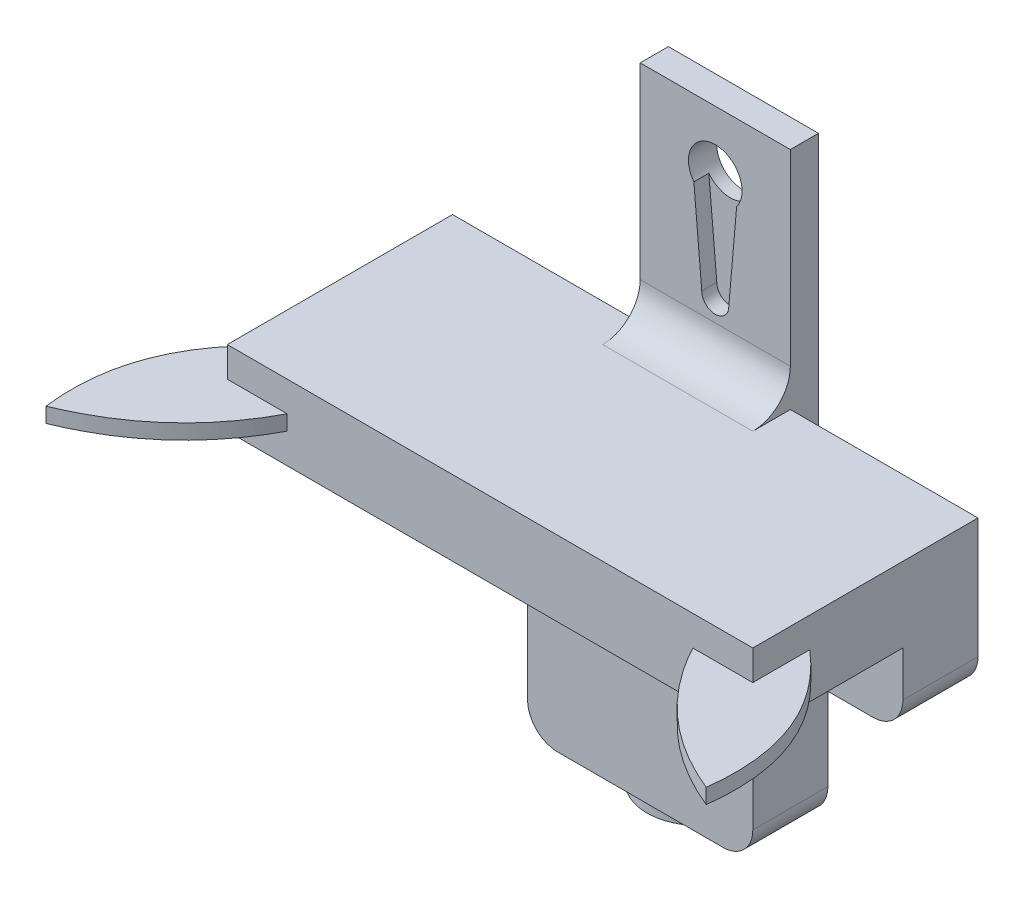
SolidWorks part; units mm, degrees
ref_plane "Front Plane" through (0, 0, 0) normal (0, 0, 1) x (1, 0, 0)
ref_plane "Top Plane" through (0, 0, 0) normal (0, 1, 0) x (1, 0, 0)
ref_plane "Right Plane" through (0, 0, 0) normal (1, 0, 0) x (0, 0, -1)
sketch "Sketch3" plane through (0, 0, 0) normal (0, 0, 1) x (1, 0, 0)
  line L1 (-10, 25) -> (10, 25)
  line L2 (-10, 25) -> (-10, -25)
  line L3 (-10, -25) -> (10, -25)
  line L4 (10, 25) -> (10, -25)
  line L5 (-10, 25) -> (10, -25) construction
  line L6 (-10, -25) -> (10, 25) construction
  point P0 (0, 0)
  dimension "D1" = 20
  dimension "D2" = 50
extrude "Boss-Extrude3" add sketch "Sketch3" along normal blind 5
sketch "Sketch4" plane through (0, 0, 5) normal (0, 0, 1) x (1, 0, 0)
  line L0 (-1.8, 2.7957) -> (1.8, 2.7957)
  line L1 (-2.85, 14.85) -> (2.85, 14.85)
  line L2 (-2.85, 14.85) -> (-1.8, 2.7957)
  line L3 (2.85, 14.85) -> (1.8, 2.7957)
  line L4 (10, -25) -> (10, 25) construction
  line L7 (10, 25) -> (-10, 25) construction
  circle A0 centre (0, 17) radius 3.57
  arc A1 (-1.8, 2.7957) -> (1.8, 2.7957) centre (0, 2.7957) ccw
  dimension "D1" = 7.14
  dimension "D2" = 3.6
  dimension "D3" = 5.7
  dimension "D4" = 12.1
  dimension "D5" = 12.1
  dimension "D6" = 10
  dimension "D7" = 8
extrude "Cut-Extrude2" cut sketch "Sketch4" against normal blind 2 contours L0 A1 | A0 L2 L0 L3
sketch "Sketch6" plane through (0, 0, 3) normal (0, 0, 1) x (1, 0, 0)
  line L0 (10, 25) -> (-10, 25) construction
  line L1 (-10, 25) -> (-10, -25) construction
  circle A0 centre (0, 17) radius 3.57
  dimension "D1" = 7.14
  dimension "D2" = 8
  dimension "D3" = 10
extrude "Cut-Extrude3" cut sketch "Sketch6" against normal blind 3
sketch "Sketch8" plane through (10, 0, 0) normal (1, 0, 0) x (0, 0, -1)
  line L6 (0, 25) -> (-1.25, 25)
  line L7 (0, 25) -> (0, -25)
  line L8 (0, -25) -> (-1.25, -25)
  line L9 (-1.25, 25) -> (-1.25, -25)
  dimension "D2" = 1.25
extrude "Cut-Extrude5" cut sketch "Sketch8" against normal blind 30
sketch "Sketch9" plane through (0, 0, 5) normal (0, 0, 1) x (1, 0, 0)
  line L1 (-35, -25) -> (35, -25)
  line L2 (-35, -25) -> (-35, -5)
  line L3 (-35, -5) -> (35, -5)
  line L4 (35, -25) -> (35, -5)
  line L5 (-10, 25) -> (-10, -25) construction
  dimension "D1" = 20
  dimension "D2" = 70
  dimension "D3" = 25
extrude "Boss-Extrude4" add sketch "Sketch9" along normal blind 20
sketch "Sketch10" plane through (0, 0, 25) normal (0, 0, 1) x (1, 0, 0)
  line L0 (35, -25) -> (35, -5) construction
  line L1 (-35, -25) -> (35, -25)
  line L2 (-35, -25) -> (-35, -15)
  line L3 (-35, -15) -> (35, -15)
  line L4 (35, -25) -> (35, -15)
  dimension "D1" = 10
  dimension "D2" = 70
extrude "Cut-Extrude6" cut sketch "Sketch10" against normal blind 10
sketch "Sketch11" plane through (0, -25, 0) normal (0, -1, 0) x (-1, 0, 0)
  line L1 (15, -15) -> (-15, -15)
  line L2 (15, -15) -> (15, -5)
  line L3 (15, -5) -> (-15, -5)
  line L4 (-15, -15) -> (-15, -5)
  line L9 (35, -15) -> (35, -5) construction
  dimension "D1" = 10
  dimension "D2" = 30
  dimension "D3" = 20
extrude "Boss-Extrude5" add sketch "Sketch11" along normal blind 25
sketch "Sketch12" plane through (0, 0, 15) normal (0, 0, 1) x (1, 0, 0)
  line L1 (-10, -15) -> (10, -15)
  line L2 (-10, -15) -> (-10, -16.5)
  line L3 (-10, -16.5) -> (10, -16.5)
  line L4 (10, -15) -> (10, -16.5)
  line L5 (35, -25) -> (35, -15) construction
  dimension "D1" = 1.5
  dimension "D2" = 25
  dimension "D3" = 20
extrude "Cut-Extrude7" cut sketch "Sketch12" against normal blind 1
sketch "Sketch13" plane through (0, -5, 0) normal (0, 1, 0) x (1, 0, 0)
  line L1 (7.5, 20.8069) -> (-7.5, 20.8069)
  line L2 (7.5, 20.8069) -> (7.5, -18)
  line L3 (7.5, -18) -> (-7.5, -18)
  line L4 (-7.5, 20.8069) -> (-7.5, -18)
  line L5 (35, -25) -> (35, -5) construction
  dimension "D2" = 15
  dimension "D3" = 27.5
extrude "Cut-Extrude8" cut sketch "Sketch13" against normal blind 13
sketch "Sketch15" plane through (0, -50, 0) normal (0, -1, 0) x (1, 0, 0)
  line L0 (0, 7.1) -> (5.5535, 11.3613)
  line L1 (0, 7.1) -> (-5.5535, 11.3613)
  line L2 (15, 5) -> (15, 15) construction
  line L3 (-15, 5) -> (15, 5) construction
  line L4 (-10, 5) -> (10, 5) construction
  arc A0 (5.5535, 11.3613) -> (-5.5535, 11.3613) centre (0, 7.1) ccw
  dimension "D1" = 7
  dimension "D2" = 7
  dimension "D3" = 15
  dimension "D4" = 105
  dimension "D5" = 2.1
  dimension "D6" = 37.5
extrude "Boss-Extrude6" add sketch "Sketch15" along normal blind 2
sketch "Sketch16" plane through (0, -52, 0) normal (0, -1, 0) x (-1, 0, 0)
  line L0 (0, -6.1037) -> (0, -16.4462) construction
  circle A0 centre (-1.5, -11.4985) radius 0.75
  circle A2 centre (1.5, -11.4985) radius 0.75
  dimension "D1" = 1.5
  dimension "D2" = 1.5
extrude "Cut-Extrude9" cut sketch "Sketch16" against normal blind 0.5
sketch "Sketch17" plane through (0, 0, 25) normal (0, 0, 1) x (1, 0, 0)
  line L0 (-35, -11) -> (35, -11) construction
  line L1 (-35, -5) -> (-35, -15) construction
  line L2 (35, -15) -> (35, -5) construction
  line L3 (35, -15) -> (-35, -15) construction
  dimension "D1" = 4
ref_plane "Plane1" through (0, -11, 0) normal (0, -1, 0) x (-1, 0, 0)
sketch "Sketch19" plane through (0, 0, 25) normal (0, 0, 1) x (1, 0, 0)
  line L1 (-35, -5) -> (35, -5)
  line L2 (-35, -5) -> (-35, -15)
  line L3 (-35, -15) -> (35, -15)
  line L4 (35, -5) -> (35, -15)
extrude "Boss-Extrude8" add sketch "Sketch19" along normal blind 10
sketch "Sketch21" plane through (0, -11, 0) normal (0, -1, 0) x (-1, 0, 0)
  line L0 (-24.9546, -30.3511) -> (-33.4675, -26.1826)
  line L1 (0, 0) -> (0, -50.4327) construction
  line L2 (24.9546, -30.3511) -> (33.4675, -26.1826)
  spline S0 degree 2 poles (-24.9546, -30.3511) (-30.2103, -44.5601) (-43.9755, -50.1793) knots 0 0 0 1 1 1
  spline S1 degree 2 poles (-33.4675, -26.1826) (-45.8092, -35.5875) (-43.9755, -50.1793) knots 0 0 0 1 1 1
  spline S2 degree 2 poles (24.9546, -30.3511) (30.2103, -44.5601) (43.9755, -50.1793) knots 0 0 0 1 1 1
  spline S3 degree 2 poles (33.4675, -26.1826) (45.8092, -35.5875) (43.9755, -50.1793) knots 0 0 0 1 1 1
extrude "Boss-Extrude9" add sketch "Sketch21" against normal blind 2
fillet "Fillet1" radius 6 2 edges at (15, -25, 10) (-15, -25, 10)
fillet "Fillet2" radius 4 4 edges at (-35, -25, 10) (-15, -50, 10) (15, -50, 10) (35, -25, 10)
sketch "Sketch22" plane through (0, 0, 1.25) normal (0, 0, -1) x (-1, 0, 0)
  line L0 (7.5, -5) -> (7.5, -18) construction
  line L1 (-7.5, -5) -> (7.5, -5)
  line L2 (-7.5, -5) -> (-7.5, -10)
  line L3 (-7.5, -10) -> (7.5, -10)
  line L4 (7.5, -5) -> (7.5, -10)
  dimension "D1" = 5
extrude "Boss-Extrude10" add sketch "Sketch22" against normal blind 25
fillet "Fillet3" radius 5 1 edges at (0, -5, 5)
